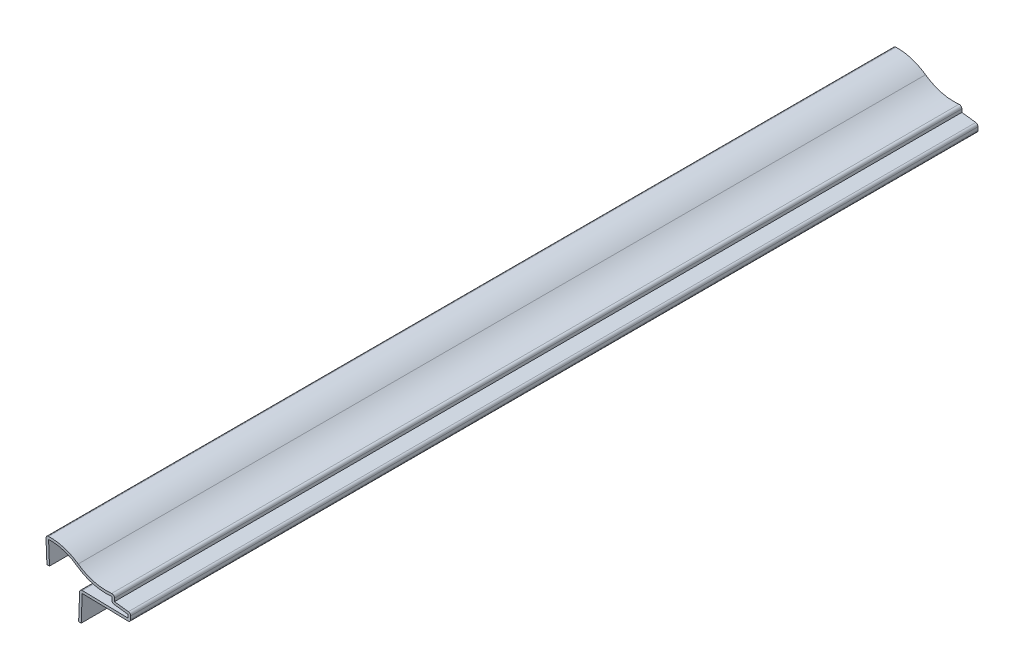
SolidWorks part; units mm, degrees
ref_plane "Front Plane" through (0, 0, 0) normal (0, 0, 1) x (1, 0, 0)
ref_plane "Top Plane" through (0, 0, 0) normal (0, 1, 0) x (1, 0, 0)
ref_plane "Right Plane" through (0, 0, 0) normal (1, 0, 0) x (0, 0, -1)
sketch "Sketch1" plane through (0, 0, 0) normal (0, 0, 1) x (1, 0, 0)
  line L0 (0, 0) -> (-0.3969, 9.9219)
  line L1 (26.5906, 3.1007) -> (26.5906, 0.7194)
  line L2 (26.5906, 0.7194) -> (32.9406, -0.0743)
  line L3 (32.9406, -0.0743) -> (32.9406, -3.2493)
  line L4 (32.9406, -3.2493) -> (13.8906, -2.8525)
  line L5 (13.8906, -2.8525) -> (13.4938, -13.1652)
  arc A0 (-0.3969, 9.9219) -> (12.3031, 6.4112) centre (1.1906, -9.0619) cw
  arc A1 (12.3031, 6.4112) -> (26.5906, 3.1007) centre (23.4156, 21.8842) ccw
  point P7 (-45.8685, -5.409)
  point P14 (1.1906, 9.9881)
  dimension "D3" = 19.05
  dimension "D4" = 19.05
  dimension "D11" = 13.2375
  dimension "D1" = 0.3969
  dimension "D2" = 33.3375
  dimension "D5" = 2.3813
  dimension "D6" = 0.7937
  dimension "D7" = 0.3969
  dimension "D8" = 9.9219
  dimension "D9" = 3.175
  dimension "D10" = 3.175
  dimension "D13" = 19.05
  dimension "D14" = 0.3969
  dimension "D15" = 10.3187
  dimension "D16" = 26.9875
extrude "Extrude-Thin1" add sketch "Sketch1" against normal blind 333.375 thin
fillet "Fillet1" radius 1.016 6 edges at (25.5746, -0.1775, -166.6875) (32.9406, -3.2493, -166.6875) (32.9406, -0.0743, -166.6875) (26.5906, 3.1007, -166.6875) (-0.3969, 9.9219, -166.6875) (12.9138, -1.8159, -166.6875)
